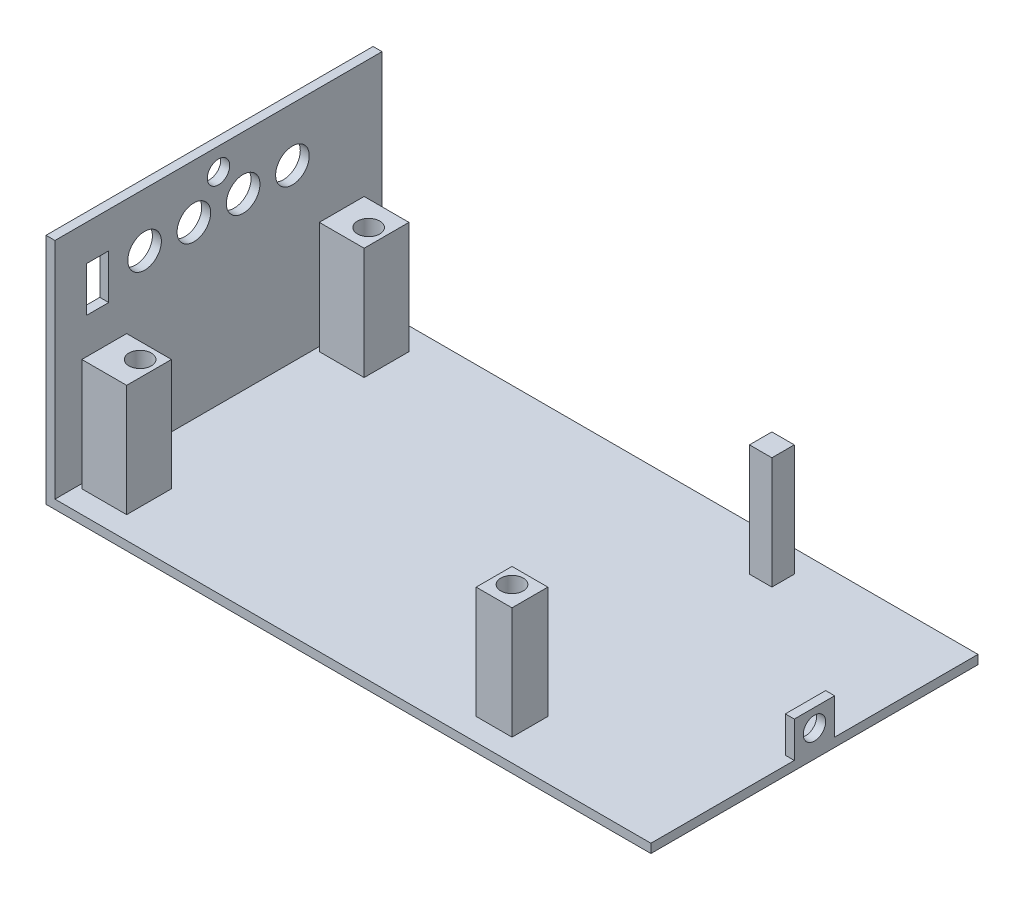
SolidWorks part; units mm, degrees
ref_plane "Front Plane" through (0, 0, 0) normal (0, 0, 1) x (1, 0, 0)
ref_plane "Top Plane" through (0, 0, 0) normal (0, 1, 0) x (1, 0, 0)
ref_plane "Right Plane" through (0, 0, 0) normal (1, 0, 0) x (0, 0, -1)
sketch "Sketch1" plane through (0, 0, 0) normal (0, 1, 0) x (1, 0, 0)
  line L1 (-67.5, -36.5) -> (67.5, -36.5)
  line L2 (-67.5, -36.5) -> (-67.5, 36.5)
  line L3 (-67.5, 36.5) -> (67.5, 36.5)
  line L4 (67.5, -36.5) -> (67.5, 36.5)
  line L5 (-67.5, -36.5) -> (67.5, 36.5) construction
  line L6 (-67.5, 36.5) -> (67.5, -36.5) construction
  point P0 (0, 0)
  dimension "D1" = 135
  dimension "D2" = 73
extrude "Boss-Extrude1" add sketch "Sketch1" along normal blind 2
sketch "Sketch2" plane through (0, 2, 0) normal (0, 1, 0) x (1, 0, 0)
  line L0 (67.5, 36.5) -> (-67.5, 36.5) construction
  line L1 (-67.5, -36.5) -> (-65.5, -36.5)
  line L2 (-67.5, -36.5) -> (-67.5, 36.5)
  line L3 (-67.5, 36.5) -> (-65.5, 36.5)
  line L4 (-65.5, -36.5) -> (-65.5, 36.5)
  dimension "D1" = 2
extrude "Boss-Extrude2" add sketch "Sketch2" along normal blind 50
sketch "Sketch4" plane through (0, 2, 0) normal (0, 1, 0) x (1, 0, 0)
  line L0 (-65.5, -36.5) -> (-65.5, 36.5) construction
  line L1 (-64.5, -31.5) -> (-54.5, -31.5)
  line L2 (-64.5, -31.5) -> (-64.5, -21.5)
  line L3 (-64.5, 31.5) -> (-54.5, 31.5)
  line L4 (31.5, -31.5) -> (31.5, -23.5)
  line L5 (-65.5, -36.5) -> (67.5, -36.5) construction
  line L6 (23.5, -31.5) -> (31.5, -31.5)
  line L7 (31.5, 31.5) -> (26.5, 31.5)
  line L8 (31.5, 31.5) -> (31.5, 26.5)
  line L9 (31.5, 26.5) -> (26.5, 26.5)
  line L10 (26.5, 31.5) -> (26.5, 26.5)
  line L11 (31.5, -31.5) -> (23.5, -31.5)
  line L12 (31.5, -31.5) -> (31.5, -23.5)
  line L13 (31.5, -23.5) -> (23.5, -23.5)
  line L14 (23.5, -31.5) -> (23.5, -23.5)
  line L15 (-64.5, -31.5) -> (-54.5, -31.5)
  line L16 (-64.5, -31.5) -> (-64.5, -21.5)
  line L17 (-64.5, -21.5) -> (-54.5, -21.5)
  line L18 (-54.5, -31.5) -> (-54.5, -21.5)
  line L19 (-64.5, 31.5) -> (-54.5, 31.5)
  line L20 (-64.5, 31.5) -> (-64.5, 21.5)
  line L21 (-64.5, 21.5) -> (-54.5, 21.5)
  line L22 (-54.5, 31.5) -> (-54.5, 21.5)
  line L23 (31.5, 26.5) -> (31.5, 31.5)
  line L24 (26.5, 31.5) -> (31.5, 31.5)
  line L25 (-64.5, 21.5) -> (-64.5, 31.5)
  circle A0 centre (-58, -25) radius 2.5
  circle A1 centre (-58, 26) radius 2.5
  circle A2 centre (27, -27) radius 2.5
  dimension "D5" = 5
  dimension "D6" = 6.5
  dimension "D10" = 5
  dimension "D11" = 5
  dimension "D1" = 96
  dimension "D2" = 63
  dimension "D3" = 1
  dimension "D4" = 5
  dimension "D7" = 6.5
  dimension "D8" = 5.5
  dimension "D9" = 6.5
  dimension "D12" = 4.5
  dimension "D13" = 4.5
  dimension "D14" = 10
  dimension "D15" = 10
  dimension "D16" = 10
  dimension "D17" = 10
  dimension "D18" = 5
  dimension "D19" = 5
  dimension "D20" = 8
  dimension "D21" = 8
extrude "Boss-Extrude4" add sketch "Sketch4" along normal blind 25 contours L14 L6 L4 L13 A2 | L1 L18 L17 L2 A0 | L22 L3 L20 L21 A1 | L7 L10 L9 L8
sketch "Sketch5" plane through (0, 2, 0) normal (0, 1, 0) x (1, 0, 0)
  line L0 (31.5, -31.5) -> (31.5, -23.5) construction
  line L1 (23.5, -31.5) -> (31.5, -31.5) construction
  circle A0 centre (9.5, -13.5) radius 2.5
  dimension "D1" = 5
  dimension "D2" = 22
  dimension "D3" = 18
extrude "Cut-Extrude1" cut sketch "Sketch5" against normal blind 2
sketch "Sketch6" plane through (-65.5, 0, 0) normal (1, 0, 0) x (0, 0, -1)
  line L0 (-36.5, 52) -> (36.5, 52) construction
  line L1 (-36.5, 52) -> (-36.5, 2) construction
  line L2 (36.5, 52) -> (36.5, 2) construction
  circle A0 centre (-16.5, 40) radius 3.75
  circle A1 centre (-5.5, 40) radius 3.75
  circle A2 centre (5.5, 40) radius 3.75
  circle A3 centre (16.5, 40) radius 3.75
  dimension "D1" = 7.5
  dimension "D2" = 7.5
  dimension "D3" = 7.5
  dimension "D4" = 7.5
  dimension "D5" = 12
  dimension "D6" = 12
  dimension "D7" = 12
  dimension "D8" = 12
  dimension "D9" = 20
  dimension "D10" = 20
  dimension "D11" = 11
  dimension "D12" = 11
extrude "Cut-Extrude2" cut sketch "Sketch6" against normal blind 2
sketch "Sketch7" plane through (-65.5, 0, 0) normal (1, 0, 0) x (0, 0, -1)
  line L0 (-36.5, 52) -> (-36.5, 2) construction
  line L1 (-29.5, 34) -> (-24.5, 34)
  line L2 (-29.5, 34) -> (-29.5, 44)
  line L3 (-29.5, 44) -> (-24.5, 44)
  line L4 (-24.5, 34) -> (-24.5, 44)
  line L5 (-36.5, 52) -> (36.5, 52) construction
  dimension "D1" = 10
  dimension "D2" = 5
  dimension "D3" = 7
  dimension "D4" = 8
extrude "Cut-Extrude3" cut sketch "Sketch7" against normal blind 2
sketch "Sketch8" plane through (0, 2, 0) normal (0, 1, 0) x (1, 0, 0)
  line L0 (67.5, -36.5) -> (67.5, 36.5) construction
  line L1 (67.5, -4.5) -> (65.5, -4.5)
  line L2 (67.5, -4.5) -> (67.5, 4.5)
  line L3 (67.5, 4.5) -> (65.5, 4.5)
  line L4 (65.5, -4.5) -> (65.5, 4.5)
  line L5 (67.5, 36.5) -> (-65.5, 36.5) construction
  line L6 (-65.5, -36.5) -> (67.5, -36.5) construction
  dimension "D1" = 2
  dimension "D2" = 32
  dimension "D3" = 32
extrude "Boss-Extrude5" add sketch "Sketch8" along normal blind 8
sketch "Sketch9" plane through (67.5, 0, 0) normal (1, 0, 0) x (0, 0, -1)
  line L0 (-4.5, 10) -> (-4.5, 2) construction
  line L1 (-36.5, 0) -> (36.5, 0) construction
  circle A0 centre (0, 6) radius 2.5
  point P2 (0, 0)
  point P5 (-4.5, 6)
  dimension "D1" = 5
  dimension "D2" = 4.5
  dimension "D3" = 6
extrude "Cut-Extrude4" cut sketch "Sketch9" against normal blind 8
sketch "Sketch10" plane through (-67.5, 0, 0) normal (-1, 0, 0) x (0, 0, 1)
  line L0 (-36.5, 52) -> (36.5, 52) construction
  line L1 (-36.5, 52) -> (-36.5, 0) construction
  circle A0 centre (0, 47) radius 2.5
  point P4 (0, 52)
  dimension "D2" = 5
  dimension "D1" = 5
  dimension "D3" = 36.5
extrude "Cut-Extrude5" cut sketch "Sketch10" against normal blind 2
